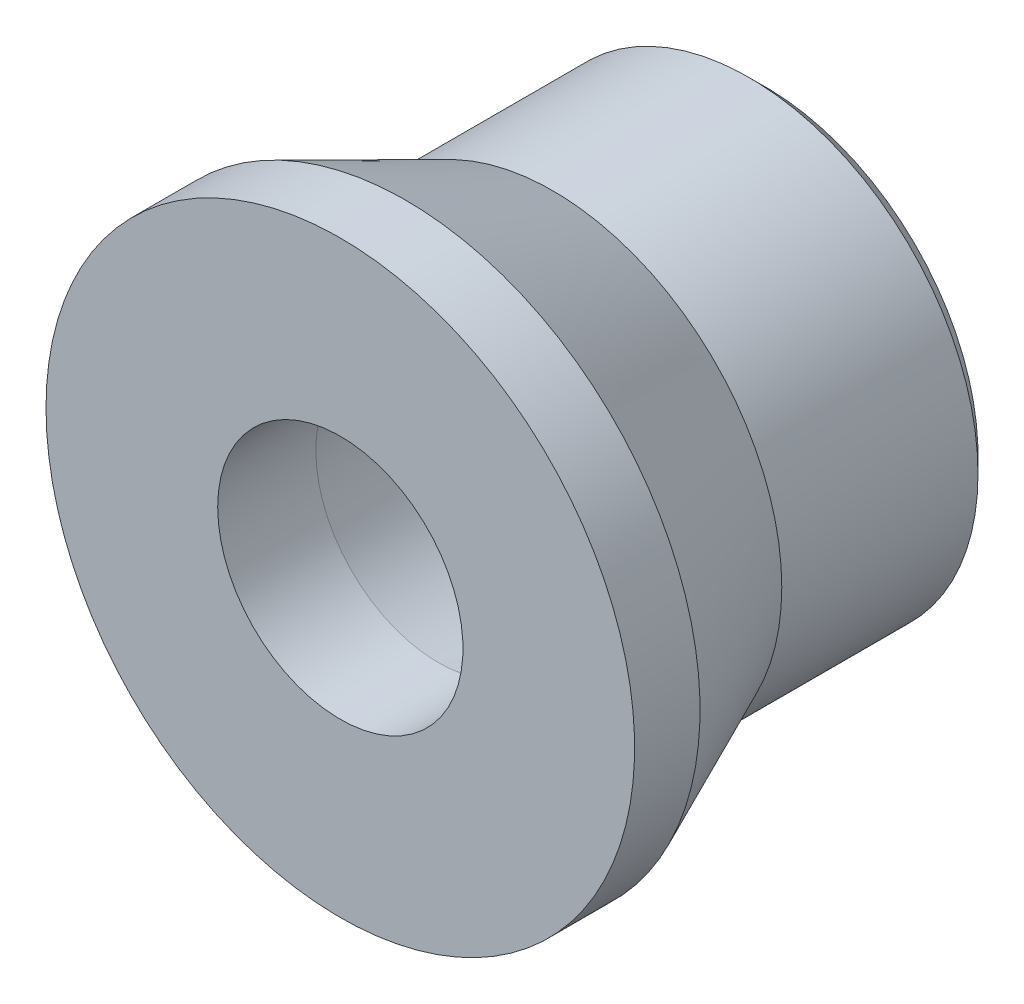
SolidWorks part; units mm, degrees
ref_plane "Front Plane" through (0, 0, 0) normal (0, 0, 1) x (1, 0, 0)
ref_plane "Top Plane" through (0, 0, 0) normal (0, 1, 0) x (1, 0, 0)
ref_plane "Right Plane" through (0, 0, 0) normal (1, 0, 0) x (0, 0, -1)
ref_plane "Plane1" through (0, 0, 0) normal (0, -1, 0) x (1, 0, 0)
sketch "Sketch1" plane through (0, 0, 0) normal (0, -1, 0) x (1, 0, 0)
  line L0 (7, 6.5) -> (9, 11)
  line L1 (9, 11) -> (9, 13)
  line L2 (9, 13) -> (3.75, 13)
  line L3 (3.75, 13) -> (3.75, 10)
  line L4 (3.75, 10) -> (5, 0)
  line L5 (5, 0) -> (6.5, 0)
  line L6 (6.5, 0) -> (7, 0.5)
  line L7 (7, 0.5) -> (7, 6.5)
  line L8 (0, 13) -> (0, 0) construction
  dimension "D1" = 3.75
  dimension "D2" = 5
  dimension "D3" = 6.5
  dimension "D4" = 7
  dimension "D5" = 9
  dimension "D6" = 0.5
  dimension "D7" = 6.5
  dimension "D8" = 10
  dimension "D9" = 11
  dimension "D10" = 13
revolve "Revolve1" add sketch "Sketch1" angle 360 about L8
